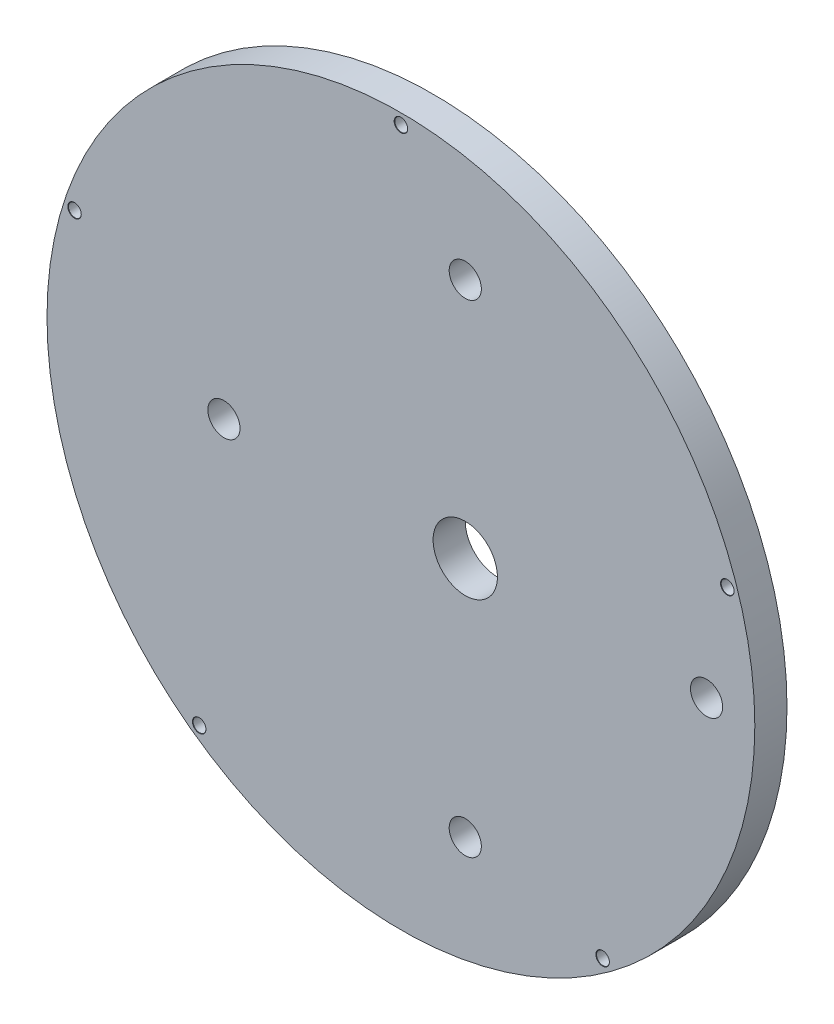
SolidWorks part; units mm, degrees
ref_plane "Front Plane" through (0, 0, 0) normal (0, 0, 1) x (1, 0, 0)
ref_plane "Top Plane" through (0, 0, 0) normal (0, 1, 0) x (1, 0, 0)
ref_plane "Right Plane" through (0, 0, 0) normal (1, 0, 0) x (0, 0, -1)
sketch "Sketch1" plane through (0, 0, 0) normal (0, 0, 1) x (1, 0, 0)
  circle A0 centre (0, 0) radius 27.5
  dimension "D1" = 55
extrude "Boss-Extrude1" add sketch "Sketch1" along normal mid plane 2.5
sketch "Sketch3" plane through (0, 0, 1.25) normal (0, 0, 1) x (1, 0, 0)
  line L0 (0, 0) -> (5, 0) construction
  circle A0 centre (5, 0) radius 2.5
  circle A1 centre (5, 0) radius 18.75 construction
  circle A2 centre (5, 18.75) radius 1.25
  circle A3 centre (-13.75, 0) radius 1.25
  circle A4 centre (23.75, 0) radius 1.25
  circle A5 centre (5, -18.75) radius 1.25
  point P16 (0, 0)
  dimension "D2" = 5
  dimension "D3" = 37.5
  dimension "D4" = 2.5
  dimension "D1" = 5
extrude "Cut-Extrude1" cut sketch "Sketch3" against normal through all both and the other way through all
sketch "Sketch4" plane through (0, 0, 1.25) normal (0, 0, 1) x (1, 0, 0)
  line L0 (0, 27.5) -> (0, 26.6667) construction
  circle A0 centre (0, 0) radius 27.5 construction
  dimension "D1" = 26.6667
hole_wizard "Ø1.0mm Dowel Hole1" positions "3DSketch1" profile "Sketch5" hole size "Ø1.0" standard "ISO" end condition through all
sketch3d "3DSketch1"
  point P0 (0, 26.6667, 1.25)
sketch "Sketch5" plane through (0, 26.6667, 1.25) normal (1, 0, 0) x (0, -1, 0)
  line L0 (0, 0) -> (0, 2.5)
  line L1 (0, 2.5) -> (0.5, 2.5)
  line L2 (0.5, 2.5) -> (0.5, 0.025)
  line L3 (0.5, 0.025) -> (0.525, 0)
  line L5 (0.525, 0) -> (0, 0)
  line L6 (-0.5, 0.025) -> (-0.525, 0) construction
  line L11 (0, -6.35) -> (0, 107.95) construction
  dimension "Thru Hole Dia." = 1
  dimension "Thru Hole Depth" = 2.5
  dimension "Near C'Sink Dia." = 1.05
  dimension "Near C'Sink Angle" = 90
pattern_circular "CirPattern1" count 5 over 360 about axis through (0, 0, 0) along (0, 0, 1) of "Ø1.0mm Dowel Hole1"
